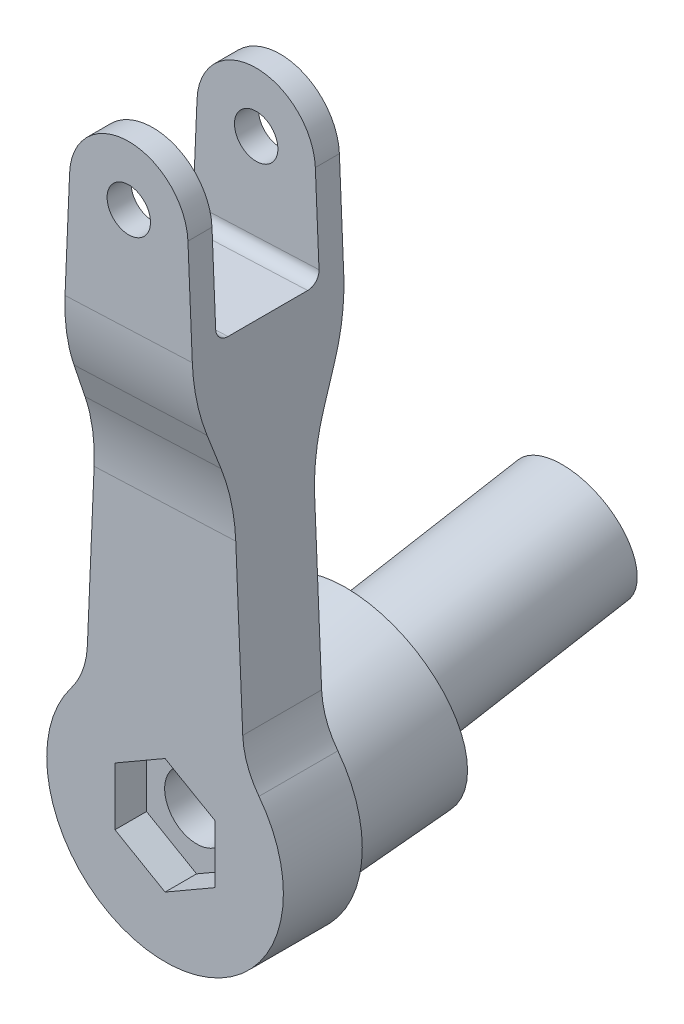
SolidWorks part; units mm, degrees
ref_plane "Front Plane" through (0, 0, 0) normal (0, 0, 1) x (1, 0, 0)
ref_plane "Top Plane" through (0, 0, 0) normal (0, 1, 0) x (1, 0, 0)
ref_plane "Right Plane" through (0, 0, 0) normal (1, 0, 0) x (0, 0, -1)
sketch "Sketch1" plane through (0, 0, 0) normal (0, 0, 1) x (1, 0, 0)
  line L0 (0, 0) -> (0, 69.866) construction
  line L1 (-7.5, 70.1838) -> (-10, 11.1803)
  line L3 (7.5, 70.1838) -> (10, 11.1803)
  arc A6 (-10, 11.1803) -> (10, 11.1803) centre (0, 0) ccw
  circle A7 centre (0, 69.866) radius 2.75
  arc A8 (-7.5, 70.1838) -> (7.5, 70.1838) centre (0, 69.866) cw
  dimension "D1" = 69.866
  dimension "D3" = 30
  dimension "D4" = 5.5
  dimension "D5" = 20
  dimension "D6" = 15
extrude "Boss-Extrude1" add sketch "Sketch1" along normal blind 19.2
sketch "Sketch13" plane through (10.4549, 0.443, 0) normal (0.9991, 0.0423, 0) x (0, 0, -1)
  line L0 (0, 77.3101) -> (-19.2, 77.3101) construction
  line L2 (-16.15, 77.3101) -> (-16.15, 57.3101)
  line L3 (-16.15, 57.3101) -> (-3.05, 57.3101)
  line L4 (-3.05, 77.3101) -> (-3.05, 57.3101)
  line L5 (-16.15, 77.3101) -> (-3.05, 57.3101) construction
  line L6 (-16.15, 57.3101) -> (-3.05, 77.3101) construction
  line L7 (-19.2, 77.3101) -> (-16.15, 77.3101) construction
  line L8 (-19.2, 10.747) -> (-19.2, 69.8034) construction
  line L9 (0, 10.747) -> (0, 69.8034) construction
  line L10 (-19.2, 52.3101) -> (-14.6, 39.6717)
  line L11 (-19.2, 10.747) -> (-19.2, 69.8034) construction
  line L12 (-14.6, 39.6717) -> (-14.6, -15)
  line L13 (-19.2, -15) -> (0, -15) construction
  line L14 (-19.2, 52.3101) -> (-19.2, 77.3101)
  line L15 (-19.2, 77.3101) -> (-16.15, 77.3101)
  line L16 (-9.6, 65.3081) -> (-9.6, -49934.6919) construction
  line L17 (0, 77.3101) -> (-3.05, 77.3101)
  line L18 (0, 52.3101) -> (0, 77.3101)
  line L19 (0, 52.3101) -> (-4.6, 39.6717)
  line L20 (-4.6, 39.6717) -> (-4.6, -15)
  line L21 (-3.05, 77.3101) -> (0, 77.3101) construction
  line L22 (-14.6, -15) -> (-4.6, -15)
  point P4 (-9.6, 67.3101)
  dimension "D1" = 3.05
  dimension "D2" = 20
  dimension "D3" = 160
  dimension "D4" = 5
  dimension "D5" = 10
extrude "Cut-Extrude4" cut sketch "Sketch13" against normal through all both and the other way through all flip side to cut
sketch "Sketch3" plane through (0, 0, 14.6) normal (0, 0, 1) x (1, 0, 0)
  line L1 (0, 7.3323) -> (-6.35, 3.6662)
  line L2 (-6.35, 3.6662) -> (-6.35, -3.6662)
  line L3 (-6.35, -3.6662) -> (0, -7.3323)
  line L4 (0, -7.3323) -> (6.35, -3.6662)
  line L5 (6.35, -3.6662) -> (6.35, 3.6662)
  line L6 (6.35, 3.6662) -> (0, 7.3323)
  circle A0 centre (0, 0) radius 6.35 construction
  dimension "D1" = 12.7
extrude "Cut-Extrude2" cut sketch "Sketch3" against normal blind 4
sketch "Sketch5" plane through (0, 0, 0) normal (1, 0, 0) x (0, 0, -1)
  line L0 (-5, 0) -> (10.4, 2.7154) construction
  line L1 (0, 52.7062) -> (0, 70.1838) construction
  line L2 (-4.6, 40.0791) -> (-4.6, 11.1803) construction
  line L3 (0, 52.7062) -> (0, 70.1838) construction
  point P13 (10.4, 2.7154)
  dimension "D1" = 10
  dimension "D2" = 5
  dimension "D3" = 15
ref_plane "Plane3" through (0, 2.7154, -10.4) normal (0, 0.1736, -0.9848) x (-1, 0, 0)
sketch "Sketch9" plane through (0, 2.7154, -10.4) normal (0, 0.1736, -0.9848) x (-1, 0, 0)
  circle A0 centre (0, -0.8682) radius 13
  circle A2 centre (0, -0.8682) radius 11 construction
  dimension "D1" = 22
  dimension "D2" = 2
sketch "Sketch4" plane through (0, 0, 10.6) normal (0, 0, 1) x (1, 0, 0)
  circle A0 centre (0, 0) radius 4.05
  dimension "D1" = 8.1
extrude "Cut-Extrude3" cut sketch "Sketch4" against normal blind 20
fillet "Fillet4" radius 10 2 edges at (-10, 11.1803, 9.6) (10, 11.1803, 9.6)
extrude "Boss-Extrude2" add sketch "Sketch9" against normal up to surface (13.0922 mm away)
sketch "Sketch10" plane through (0, 1.8604, -10.5508) normal (0, 0.1736, -0.9848) x (-1, 0, 0)
  circle A0 centre (0, 0) radius 8
  dimension "D1" = 16
extrude "Boss-Extrude3" add sketch "Sketch10" along normal blind 27
draft "Draft1" type of draft neutral plane draft angle 3 faces to draft 1 face at (0, 12.3894, 4.6) neutral plane through (0, 1.8604, -10.5508) neutral plane normal (0, 0.1736, -0.9848) reverse direction yes parameters "D1"=3
fillet "Fillet5" radius 25 4 edges at (-0.0148, 52.3564, 0) (-0.0158, 39.7066, 4.6) (-0.0158, 39.7066, 14.6) (-0.0148, 52.3564, 19.2)
sketch "Sketch14" plane through (0, 6.5489, -37.1406) normal (0, 0.1736, -0.9848) x (-1, 0, 0)
  line L0 (0, 0) -> (0, -8) construction
  circle A0 centre (-3.4641, 2) radius 2
  circle A1 centre (3.4641, 2) radius 2
  circle A2 centre (0, -4) radius 2
  circle A4 centre (0, 0) radius 8
  circle A5 centre (0, 0) radius 8 construction
  point P9 (0, 0)
  point P10 (0, -4)
  dimension "D1" = 4
  dimension "D2" = 0
  dimension "D4" = 3
extrude "Cut-Extrude5" cut sketch "Sketch14" against normal blind 4
fillet "Fillet6" radius 1.5 3 edges at (0, 11.6862, 4.6) (-0.0144, 57.3609, 3.05) (-0.0144, 57.3609, 16.15)
equation "\"Leg_Tilt\"=10"
equation "\"D1@Sketch5\"=\"Leg_Tilt\""
